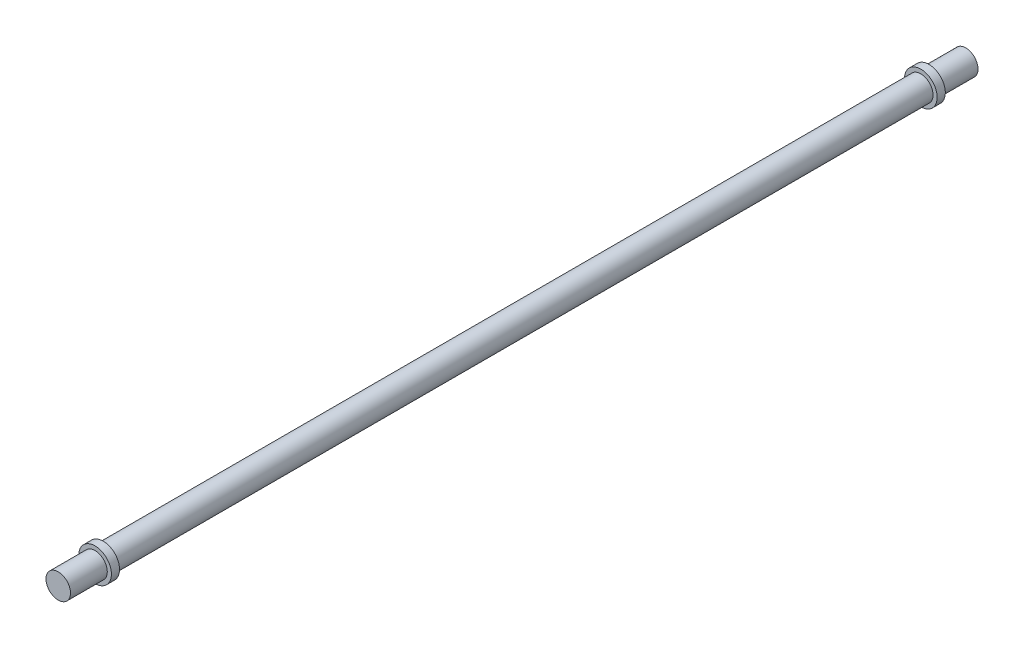
SolidWorks part; units mm, degrees
ref_plane "Front" through (0, 0, 0) normal (0, 0, 1) x (1, 0, 0)
ref_plane "Top" through (0, 0, 0) normal (0, 1, 0) x (1, 0, 0)
ref_plane "Right" through (0, 0, 0) normal (1, 0, 0) x (0, 0, -1)
sketch "Sketch1" plane through (0, 0, 0) normal (0, 0, 1) x (1, 0, 0)
  circle A0 centre (0, 0) radius 15
  dimension "D1" = 30
extrude "Boss-Extrude1" add sketch "Sketch1" along normal blind 1000
sketch "Sketch2" plane through (0, 0, 1000) normal (0, 0, 1) x (1, 0, 0)
  circle A0 centre (0, 0) radius 20
extrude "Boss-Extrude2" add sketch "Sketch2" along normal blind 10
sketch "Sketch3" plane through (0, 0, 1010) normal (0, 0, 1) x (1, 0, 0)
  circle A0 centre (0, 0) radius 15
extrude "Boss-Extrude3" add sketch "Sketch3" along normal blind 45
sketch "Sketch4" plane through (0, 0, 0) normal (0, 0, -1) x (-1, 0, 0)
  circle A0 centre (0, 0) radius 20 construction
  circle A1 centre (0, 0) radius 20
extrude "Boss-Extrude4" add sketch "Sketch4" along normal blind 10
sketch "Sketch5" plane through (0, 0, -10) normal (0, 0, -1) x (-1, 0, 0)
  circle A0 centre (0, 0) radius 15 construction
  circle A1 centre (0, 0) radius 15
extrude "Boss-Extrude5" add sketch "Sketch5" along normal blind 45
